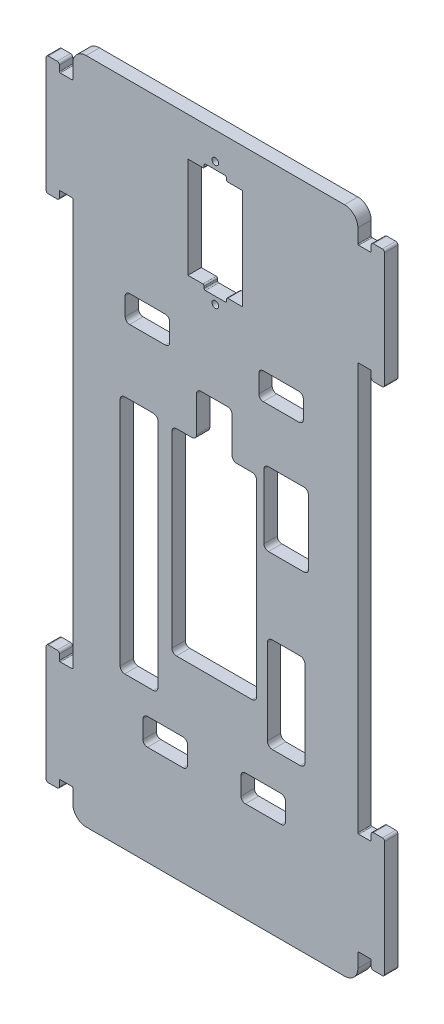
SolidWorks part; units mm, degrees
ref_plane "前视基准面" through (0, 0, 0) normal (0, 0, 1) x (1, 0, 0)
ref_plane "上视基准面" through (0, 0, 0) normal (0, 1, 0) x (1, 0, 0)
ref_plane "右视基准面" through (0, 0, 0) normal (1, 0, 0) x (0, 0, -1)
sketch "草图1" plane through (0, 0, 0) normal (0, 0, 1) x (1, 0, 0)
  line L0 (32.2, 68.7) -> (34.8, 68.7)
  line L1 (-29, 75) -> (29, 75)
  line L2 (-32, 72) -> (-32, -72) construction
  line L3 (-29, -75) -> (29, -75)
  line L4 (32, 72) -> (32, -72) construction
  line L5 (-32, 75) -> (32, -75) construction
  line L6 (-32, -75) -> (32, 75) construction
  line L7 (35, 68.9) -> (35, 70.15)
  line L8 (35.5, 70.65) -> (37.5, 70.65)
  line L9 (38, 70.15) -> (38, 44.35)
  line L10 (37.5, 43.85) -> (35.5, 43.85)
  line L11 (35, 44.35) -> (35, 45.6)
  line L12 (34.8, 45.8) -> (32.2, 45.8)
  line L13 (38, 57.25) -> (32, 57.25) construction
  line L14 (32, 68.9) -> (32, 72)
  line L15 (32, 45.6) -> (32, -45.6)
  line L16 (0, 0) -> (19.5271, 0) construction
  line L17 (0, 0) -> (0, 19.9471) construction
  line L18 (34.8, -45.8) -> (32.2, -45.8)
  line L19 (35, -44.35) -> (35, -45.6)
  line L20 (37.5, -43.85) -> (35.5, -43.85)
  line L21 (32, -68.9) -> (32, -72)
  line L22 (32.2, -68.7) -> (34.8, -68.7)
  line L23 (35, -68.9) -> (35, -70.15)
  line L24 (35.5, -70.65) -> (37.5, -70.65)
  line L25 (38, -70.15) -> (38, -44.35)
  line L26 (-37.5, 43.85) -> (-35.5, 43.85)
  line L27 (-35, 44.35) -> (-35, 45.6)
  line L28 (-34.8, 45.8) -> (-32.2, 45.8)
  line L29 (-32, 45.6) -> (-32, -45.6)
  line L30 (-34.8, -45.8) -> (-32.2, -45.8)
  line L31 (-35, -44.35) -> (-35, -45.6)
  line L32 (-37.5, -43.85) -> (-35.5, -43.85)
  line L33 (-38, -70.15) -> (-38, -44.35)
  line L34 (-35.5, -70.65) -> (-37.5, -70.65)
  line L35 (-35, -68.9) -> (-35, -70.15)
  line L36 (-32.2, -68.7) -> (-34.8, -68.7)
  line L37 (-32, -68.9) -> (-32, -72)
  line L38 (-37.5, 43.85) -> (-35.5, 43.85)
  line L39 (-32, 68.9) -> (-32, 72)
  line L40 (-32.2, 68.7) -> (-34.8, 68.7)
  line L41 (-35, 68.9) -> (-35, 70.15)
  line L42 (-35.5, 70.65) -> (-37.5, 70.65)
  line L43 (-38, 70.15) -> (-38, 44.35)
  arc A0 (-32, -72) -> (-29, -75) centre (-29, -72) ccw
  arc A1 (29, -75) -> (32, -72) centre (29, -72) ccw
  arc A2 (29, 75) -> (32, 72) centre (29, 72) cw
  arc A3 (-32, 72) -> (-29, 75) centre (-29, 72) cw
  arc A4 (35, 70.15) -> (35.5, 70.65) centre (35.5, 70.15) cw
  arc A5 (35, 44.35) -> (35.5, 43.85) centre (35.5, 44.35) ccw
  arc A6 (37.5, 43.85) -> (38, 44.35) centre (37.5, 44.35) ccw
  arc A7 (37.5, 70.65) -> (38, 70.15) centre (37.5, 70.15) cw
  arc A8 (37.5, 43.85) -> (38, 44.35) centre (37.5, 44.35) ccw
  arc A9 (34.8, 45.8) -> (35, 45.6) centre (34.8, 45.6) cw
  arc A10 (34.8, 68.7) -> (35, 68.9) centre (34.8, 68.9) ccw
  arc A11 (32, 45.6) -> (32.2, 45.8) centre (32.2, 45.6) cw
  arc A12 (32, 68.9) -> (32.2, 68.7) centre (32.2, 68.9) ccw
  arc A13 (32, -45.6) -> (32.2, -45.8) centre (32.2, -45.6) ccw
  arc A14 (34.8, -45.8) -> (35, -45.6) centre (34.8, -45.6) ccw
  arc A15 (35, -44.35) -> (35.5, -43.85) centre (35.5, -44.35) cw
  arc A16 (32, -68.9) -> (32.2, -68.7) centre (32.2, -68.9) cw
  arc A17 (34.8, -68.7) -> (35, -68.9) centre (34.8, -68.9) cw
  arc A18 (35, -70.15) -> (35.5, -70.65) centre (35.5, -70.15) ccw
  arc A19 (37.5, -70.65) -> (38, -70.15) centre (37.5, -70.15) ccw
  arc A20 (37.5, -43.85) -> (38, -44.35) centre (37.5, -44.35) cw
  arc A21 (-35, 44.35) -> (-35.5, 43.85) centre (-35.5, 44.35) cw
  arc A22 (-34.8, 45.8) -> (-35, 45.6) centre (-34.8, 45.6) ccw
  arc A23 (-32, 45.6) -> (-32.2, 45.8) centre (-32.2, 45.6) ccw
  arc A24 (-32, -45.6) -> (-32.2, -45.8) centre (-32.2, -45.6) cw
  arc A25 (-34.8, -45.8) -> (-35, -45.6) centre (-34.8, -45.6) cw
  arc A26 (-35, -44.35) -> (-35.5, -43.85) centre (-35.5, -44.35) ccw
  arc A27 (-37.5, -43.85) -> (-38, -44.35) centre (-37.5, -44.35) ccw
  arc A28 (-37.5, -70.65) -> (-38, -70.15) centre (-37.5, -70.15) cw
  arc A29 (-35, -70.15) -> (-35.5, -70.65) centre (-35.5, -70.15) cw
  arc A30 (-34.8, -68.7) -> (-35, -68.9) centre (-34.8, -68.9) ccw
  arc A31 (-32, -68.9) -> (-32.2, -68.7) centre (-32.2, -68.9) ccw
  arc A32 (-37.5, 43.85) -> (-38, 44.35) centre (-37.5, 44.35) cw
  arc A33 (-32, 68.9) -> (-32.2, 68.7) centre (-32.2, 68.9) cw
  arc A34 (-34.8, 68.7) -> (-35, 68.9) centre (-34.8, 68.9) cw
  arc A35 (-35, 70.15) -> (-35.5, 70.65) centre (-35.5, 70.15) ccw
  arc A36 (-37.5, 70.65) -> (-38, 70.15) centre (-37.5, 70.15) ccw
  point P0 (0, 0)
  point P33 (35, 69.525)
  point P45 (32, 45.8)
  point P53 (32, 68.7)
  point P75 (32, 0)
  point P77 (38, -57.25)
  dimension "D3" = 3
  dimension "D6" = 0.2
  dimension "D7" = 0.5
  dimension "D8" = 0.2
  dimension "D11" = 0.2
  dimension "D1" = 64
  dimension "D2" = 150
  dimension "D4" = 22.9
  dimension "D5" = 26.8
  dimension "D9" = 3
  dimension "D10" = 3
  dimension "D12" = 114.5
extrude "凸台-拉伸1" add sketch "草图1" along normal mid plane 3 contours L42 A36 L43 A32 L26 A21 L27 A22 L28 A23 L29 A24 L30 A25 L31 A26 L32 A27 L33 A28 L34 A29 L35 A30 L36 A31 L37 A0 L3 A1 L21 A16 L22 A17 L23 A18 L24 A19 L25 A20 L20 A15 L19 A14 L18 A13 L15 A11 L12 A9 L11
sketch "草图2" plane through (0, 0, 1.5) normal (0, 0, 1) x (1, 0, 0)
  line L0 (0, 0) -> (0, 55) construction
  line L1 (-6.15, 66.3) -> (6.15, 66.3)
  line L2 (-6.15, 66.3) -> (-6.15, 43.7)
  line L3 (-6.15, 43.7) -> (6.15, 43.7)
  line L4 (6.15, 66.3) -> (6.15, 43.7)
  line L5 (-6.15, 66.3) -> (6.15, 43.7) construction
  line L6 (-6.15, 43.7) -> (6.15, 66.3) construction
  line L7 (0, 55) -> (15.3315, 55) construction
  circle A0 centre (0, 41.1) radius 0.75
  circle A1 centre (0, 68.9) radius 0.75
  point P0 (0, 55)
  dimension "D3" = 1.5
  dimension "D1" = 22.6
  dimension "D2" = 12.3
  dimension "D4" = 27.8
  dimension "D5" = 55
extrude "切除-拉伸1" cut sketch "草图2" against normal through all
sketch "草图3" plane through (0, 0, 1.5) normal (0, 0, 1) x (1, 0, 0)
  line L0 (-2.5, 66.3) -> (-2.5, 67.3)
  line L1 (6.15, 66.3) -> (-6.15, 66.3) construction
  line L2 (-2.5, 67.3) -> (2.5, 67.3)
  line L3 (2.5, 67.3) -> (2.5, 66.3)
  line L4 (0, 66.3) -> (0, 63.4083) construction
  line L5 (-2.5, 66.3) -> (2.5, 66.3)
  line L6 (6.15, 55) -> (13.9493, 55) construction
  line L7 (6.15, 43.7) -> (6.15, 66.3) construction
  line L8 (-2.5, 43.7) -> (-2.5, 42.7)
  line L9 (-2.5, 42.7) -> (2.5, 42.7)
  line L10 (2.5, 42.7) -> (2.5, 43.7)
  line L11 (-2.5, 43.7) -> (2.5, 43.7)
  dimension "D1" = 1
  dimension "D2" = 5
extrude "切除-拉伸2" cut sketch "草图3" against normal through all
fillet "圆角1" radius 0.3 8 edges at (2.5, 43.7, 0) (2.5, 42.7, 0) (-2.5, 43.7, 0) (-2.5, 42.7, 0) (2.5, 66.3, 0) (2.5, 67.3, 0) (-2.5, 67.3, 0) (-2.5, 66.3, 0)
sketch "草图4" plane through (0, 0, 1.5) normal (0, 0, 1) x (1, 0, 0)
  line L0 (32, 45.6) -> (32, -45.6) construction
  line L1 (-20.36, 12.99) -> (-13.89, 12.99)
  line L2 (-21.36, 11.99) -> (-21.36, -39.9)
  line L3 (-20.36, -40.9) -> (-13.89, -40.9)
  line L4 (-12.89, 11.99) -> (-12.89, -39.9)
  line L5 (-21.36, 12.99) -> (-12.89, -40.9) construction
  line L6 (-21.36, -40.9) -> (-12.89, 12.99) construction
  line L7 (-8.74, 12.6) -> (8.26, 12.6)
  line L8 (-9.74, 11.6) -> (-9.74, -30.6)
  line L9 (-8.74, -31.6) -> (8.26, -31.6)
  line L10 (9.26, 11.6) -> (9.26, -30.6)
  line L11 (-9.74, 12.6) -> (9.26, -31.6) construction
  line L12 (-9.74, -31.6) -> (9.26, 12.6) construction
  line L13 (11.91, 15.53) -> (19.91, 15.53)
  line L14 (10.91, 14.53) -> (10.91, 0.03)
  line L15 (11.91, -0.97) -> (19.91, -0.97)
  line L16 (20.91, 14.53) -> (20.91, 0.03)
  line L17 (10.91, 15.53) -> (20.91, -0.97) construction
  line L18 (10.91, -0.97) -> (20.91, 15.53) construction
  line L19 (12.8018, -17.71) -> (19.0282, -17.71)
  line L20 (11.68, -18.8318) -> (11.68, -37.9082)
  line L21 (12.8018, -39.03) -> (19.0282, -39.03)
  line L22 (20.15, -18.8318) -> (20.15, -37.9082)
  line L23 (11.68, -17.71) -> (20.15, -39.03) construction
  line L24 (11.68, -39.03) -> (20.15, -17.71) construction
  line L25 (-29, -75) -> (29, -75) construction
  line L26 (-32, 45.6) -> (-32, -45.6) construction
  arc A0 (-21.36, -39.9) -> (-20.36, -40.9) centre (-20.36, -39.9) ccw
  arc A1 (-13.89, -40.9) -> (-12.89, -39.9) centre (-13.89, -39.9) ccw
  arc A2 (-12.89, 11.99) -> (-13.89, 12.99) centre (-13.89, 11.99) ccw
  arc A3 (-20.36, 12.99) -> (-21.36, 11.99) centre (-20.36, 11.99) ccw
  arc A4 (-8.74, 12.6) -> (-9.74, 11.6) centre (-8.74, 11.6) ccw
  arc A5 (-9.74, -30.6) -> (-8.74, -31.6) centre (-8.74, -30.6) ccw
  arc A6 (8.26, -31.6) -> (9.26, -30.6) centre (8.26, -30.6) ccw
  arc A7 (9.26, 11.6) -> (8.26, 12.6) centre (8.26, 11.6) ccw
  arc A8 (19.91, 15.53) -> (20.91, 14.53) centre (19.91, 14.53) cw
  arc A9 (20.91, 0.03) -> (19.91, -0.97) centre (19.91, 0.03) cw
  arc A10 (11.91, -0.97) -> (10.91, 0.03) centre (11.91, 0.03) cw
  arc A11 (10.91, 14.53) -> (11.91, 15.53) centre (11.91, 14.53) cw
  arc A12 (11.68, -37.9082) -> (12.8018, -39.03) centre (12.8018, -37.9082) ccw
  arc A13 (19.0282, -39.03) -> (20.15, -37.9082) centre (19.0282, -37.9082) ccw
  arc A14 (20.15, -18.8318) -> (19.0282, -17.71) centre (19.0282, -18.8318) ccw
  arc A15 (11.68, -18.8318) -> (12.8018, -17.71) centre (12.8018, -18.8318) cw
  point P0 (-17.125, -13.955)
  point P17 (-0.24, -9.5)
  point P22 (15.91, 7.28)
  point P27 (15.915, -28.37)
  dimension "D3" = 1
  dimension "D8" = 1
  dimension "D13" = 1
  dimension "D18" = 1.1218
  dimension "D1" = 53.89
  dimension "D2" = 8.47
  dimension "D4" = 10.64
  dimension "D5" = 34.1
  dimension "D6" = 19
  dimension "D7" = 44.2
  dimension "D9" = 43.4
  dimension "D10" = 22.26
  dimension "D11" = 16.5
  dimension "D12" = 10
  dimension "D14" = 11.09
  dimension "D15" = 74.03
  dimension "D16" = 21.32
  dimension "D17" = 8.47
  dimension "D19" = 11.85
  dimension "D20" = 35.97
extrude "切除-拉伸3" cut sketch "草图4" against normal through all
sketch "草图5" plane through (0, 0, 1.5) normal (0, 0, 1) x (1, 0, 0)
  line L0 (-0.24, 12.6) -> (-0.24, 22.6) construction
  line L1 (8.26, 12.6) -> (-8.74, 12.6) construction
  line L3 (-3.24, 22.6) -> (2.76, 22.6)
  line L4 (3.76, 21.6) -> (3.76, 12.6)
  line L5 (-4.24, 21.6) -> (-4.24, 12.6)
  line L6 (3.76, 12.6) -> (-4.24, 12.6)
  arc A0 (3.76, 21.6) -> (2.76, 22.6) centre (2.76, 21.6) ccw
  arc A1 (-3.24, 22.6) -> (-4.24, 21.6) centre (-3.24, 21.6) ccw
  point P11 (3.76, 22.6)
  point P14 (-4.24, 22.6)
  dimension "D3" = 1
  dimension "D1" = 10
  dimension "D2" = 8
extrude "切除-拉伸4" cut sketch "草图5" against normal through all
fillet "圆角2" radius 1 2 edges at (3.76, 12.6, 0) (-4.24, 12.6, 0)
sketch "草图6" plane through (0, 0, 1.5) normal (0, 0, 1) x (1, 0, 0)
  line L0 (-0.24, 22.6) -> (-0.24, 29.3114) construction
  line L1 (10.76, 33.6) -> (18.76, 33.6)
  line L2 (9.76, 32.6) -> (9.76, 28.6)
  line L3 (10.76, 27.6) -> (18.76, 27.6)
  line L4 (19.76, 32.6) -> (19.76, 28.6)
  line L5 (9.76, 33.6) -> (19.76, 27.6) construction
  line L6 (9.76, 27.6) -> (19.76, 33.6) construction
  line L7 (2.76, 22.6) -> (-3.24, 22.6) construction
  line L8 (8.26, 12.6) -> (4.76, 12.6) construction
  line L9 (-8.74, -31.6) -> (8.26, -31.6) construction
  line L10 (6.76, -46.6) -> (14.76, -46.6)
  line L11 (5.76, -47.6) -> (5.76, -51.6)
  line L12 (6.76, -52.6) -> (14.76, -52.6)
  line L13 (15.76, -47.6) -> (15.76, -51.6)
  line L14 (5.76, -46.6) -> (15.76, -52.6) construction
  line L15 (5.76, -52.6) -> (15.76, -46.6) construction
  line L16 (-10.24, 32.6) -> (-10.24, 28.6)
  line L17 (-11.24, 33.6) -> (-19.24, 33.6)
  line L18 (-20.24, 32.6) -> (-20.24, 28.6)
  line L19 (-11.24, 27.6) -> (-19.24, 27.6)
  line L20 (-6.24, -47.6) -> (-6.24, -51.6)
  line L21 (-7.24, -46.6) -> (-15.24, -46.6)
  line L22 (-16.24, -47.6) -> (-16.24, -51.6)
  line L23 (-7.24, -52.6) -> (-15.24, -52.6)
  arc A0 (10.76, 33.6) -> (9.76, 32.6) centre (10.76, 32.6) ccw
  arc A1 (9.76, 28.6) -> (10.76, 27.6) centre (10.76, 28.6) ccw
  arc A2 (18.76, 27.6) -> (19.76, 28.6) centre (18.76, 28.6) ccw
  arc A3 (19.76, 32.6) -> (18.76, 33.6) centre (18.76, 32.6) ccw
  arc A4 (15.76, -51.6) -> (14.76, -52.6) centre (14.76, -51.6) cw
  arc A5 (6.76, -52.6) -> (5.76, -51.6) centre (6.76, -51.6) cw
  arc A6 (5.76, -47.6) -> (6.76, -46.6) centre (6.76, -47.6) cw
  arc A7 (14.76, -46.6) -> (15.76, -47.6) centre (14.76, -47.6) cw
  arc A8 (-10.24, 28.6) -> (-11.24, 27.6) centre (-11.24, 28.6) cw
  arc A9 (-11.24, 33.6) -> (-10.24, 32.6) centre (-11.24, 32.6) cw
  arc A10 (-20.24, 32.6) -> (-19.24, 33.6) centre (-19.24, 32.6) cw
  arc A11 (-19.24, 27.6) -> (-20.24, 28.6) centre (-19.24, 28.6) cw
  arc A12 (-7.24, -52.6) -> (-6.24, -51.6) centre (-7.24, -51.6) ccw
  arc A13 (-6.24, -47.6) -> (-7.24, -46.6) centre (-7.24, -47.6) ccw
  arc A14 (-15.24, -46.6) -> (-16.24, -47.6) centre (-15.24, -47.6) ccw
  arc A15 (-16.24, -51.6) -> (-15.24, -52.6) centre (-15.24, -51.6) ccw
  point P0 (14.76, 30.6)
  point P23 (10.76, -49.6)
  point P28 (10.76, -52.6)
  point P41 (10.76, -46.6)
  point P68 (-6.24, -49.6)
  point P69 (5.76, -49.6)
  dimension "D3" = 1
  dimension "D7" = 1
  dimension "D1" = 10
  dimension "D2" = 6
  dimension "D4" = 15
  dimension "D5" = 10
  dimension "D6" = 6
  dimension "D8" = 15
  dimension "D9" = 20
  dimension "D10" = 12
extrude "切除-拉伸5" cut sketch "草图6" against normal through all
